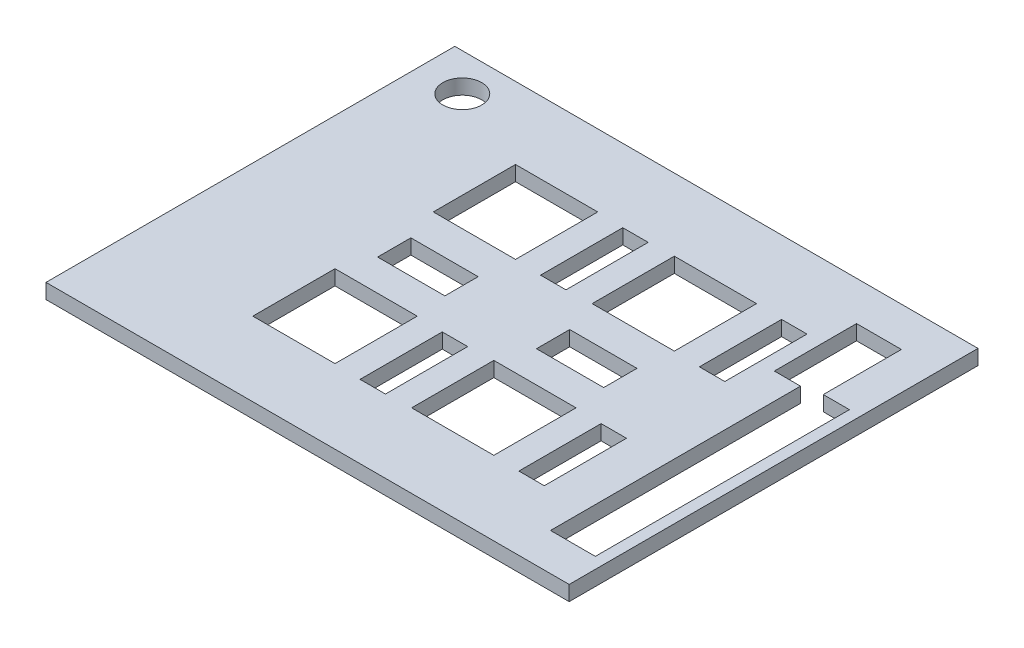
SolidWorks part; units mm, degrees
ref_plane "Front Plane" through (0, 0, 0) normal (0, 0, 1) x (1, 0, 0)
ref_plane "Top Plane" through (0, 0, 0) normal (0, 1, 0) x (1, 0, 0)
ref_plane "Right Plane" through (0, 0, 0) normal (1, 0, 0) x (0, 0, -1)
sketch "Sketch1" plane through (0, 0, 0) normal (0, 1, 0) x (1, 0, 0)
  line L0 (22.75, 28.07) -> (18.75, 28.07)
  line L1 (0, 0) -> (68, 0)
  line L2 (0, 0) -> (0, 52.7)
  line L3 (0, 52.7) -> (68, 52.7)
  line L4 (68, 0) -> (68, 52.7)
  line L5 (0, 0) -> (68, 52.7) construction
  line L6 (0, 52.7) -> (68, 0) construction
  line L7 (17.75, 43.07) -> (26.75, 43.07)
  line L8 (17.75, 43.07) -> (17.75, 34.07)
  line L9 (17.75, 34.07) -> (26.75, 34.07)
  line L10 (26.75, 43.07) -> (26.75, 34.07)
  line L11 (17.75, 43.07) -> (26.75, 34.07) construction
  line L12 (17.75, 34.07) -> (26.75, 43.07) construction
  line L13 (31.75, 33.42) -> (34.15, 33.42)
  line L14 (31.75, 33.42) -> (31.75, 43.42)
  line L15 (31.75, 43.42) -> (34.15, 43.42)
  line L16 (34.15, 33.42) -> (34.15, 43.42)
  line L17 (31.75, 33.42) -> (34.15, 43.42) construction
  line L18 (31.75, 43.42) -> (34.15, 33.42) construction
  line L19 (17.75, 18.92) -> (26.75, 18.92)
  line L20 (17.75, 18.92) -> (17.75, 9.92)
  line L21 (17.75, 9.92) -> (26.75, 9.92)
  line L22 (26.75, 18.92) -> (26.75, 9.92)
  line L23 (17.75, 18.92) -> (26.75, 9.92) construction
  line L24 (17.75, 9.92) -> (26.75, 18.92) construction
  line L25 (39, 34.07) -> (48, 34.07)
  line L26 (39, 34.07) -> (39, 43.07)
  line L27 (39, 43.07) -> (48, 43.07)
  line L28 (48, 34.07) -> (48, 43.07)
  line L29 (39, 34.07) -> (48, 43.07) construction
  line L30 (39, 43.07) -> (48, 34.07) construction
  line L31 (39, 18.92) -> (48, 18.92)
  line L32 (39, 18.92) -> (39, 9.92)
  line L33 (39, 9.92) -> (48, 9.92)
  line L34 (48, 18.92) -> (48, 9.92)
  line L35 (39, 18.92) -> (48, 9.92) construction
  line L36 (39, 9.92) -> (48, 18.92) construction
  line L37 (53, 43.42) -> (55.4, 43.42)
  line L38 (53, 43.42) -> (53, 33.42)
  line L39 (53, 33.42) -> (55.4, 33.42)
  line L40 (55.4, 43.42) -> (55.4, 33.42)
  line L41 (53, 43.42) -> (55.4, 33.42) construction
  line L42 (53, 33.42) -> (55.4, 43.42) construction
  line L43 (31.75, 19.27) -> (34.15, 19.27)
  line L44 (31.75, 19.27) -> (31.75, 9.27)
  line L45 (31.75, 9.27) -> (34.15, 9.27)
  line L46 (34.15, 19.27) -> (34.15, 9.27)
  line L47 (31.75, 19.27) -> (34.15, 9.27) construction
  line L48 (31.75, 9.27) -> (34.15, 19.27) construction
  line L49 (55.4, 19.27) -> (53, 19.27)
  line L50 (55.4, 19.27) -> (55.4, 9.27)
  line L51 (55.4, 9.27) -> (53, 9.27)
  line L52 (53, 19.27) -> (53, 9.27)
  line L53 (55.4, 19.27) -> (53, 9.27) construction
  line L54 (55.4, 9.27) -> (53, 19.27) construction
  line L55 (62, 37.5) -> (67, 37.5)
  line L56 (62, 37.5) -> (62, 4.5)
  line L57 (62, 4.5) -> (67, 4.5)
  line L58 (67, 37.5) -> (67, 4.5)
  line L59 (62, 37.5) -> (67, 4.5) construction
  line L60 (62, 4.5) -> (67, 37.5) construction
  line L61 (58.5, 47.95) -> (63.5, 47.95)
  line L62 (58.5, 47.95) -> (58.5, 37.95)
  line L63 (58.5, 37.95) -> (63.5, 37.95)
  line L64 (63.5, 47.95) -> (63.5, 37.95)
  line L65 (58.5, 47.95) -> (63.5, 37.95) construction
  line L66 (58.5, 37.95) -> (63.5, 47.95) construction
  line L67 (18.75, 24.62) -> (18.75, 28.07)
  line L68 (22.75, 28.07) -> (26.75, 28.07)
  line L69 (22.75, 24.62) -> (26.75, 24.62)
  line L70 (22.75, 24.62) -> (18.75, 24.62)
  line L71 (26.75, 24.62) -> (26.75, 28.07)
  line L73 (40, 28.07) -> (48, 28.07)
  line L74 (40, 28.07) -> (40, 24.62)
  line L75 (40, 24.62) -> (48, 24.62)
  line L76 (48, 28.07) -> (48, 24.62)
  line L77 (40, 28.07) -> (48, 24.62) construction
  line L78 (40, 24.62) -> (48, 28.07) construction
  circle A0 centre (13.75, 50.4) radius 1.5443
  circle A1 centre (13.75, 2.25) radius 1.5443
  circle A2 centre (5, 48.7) radius 1.75
  point P4 (34, 26.35)
  point P16 (22.25, 38.57)
  point P19 (32.95, 38.42)
  point P24 (22.25, 14.42)
  point P29 (43.5, 38.57)
  point P30 (39, 38.57)
  point P35 (43.5, 14.42)
  point P40 (54.2, 38.42)
  point P45 (32.95, 14.27)
  point P50 (54.2, 14.27)
  point P57 (64.5, 21)
  point P62 (61, 42.95)
  point P64 (22.25, 34.07)
  point P74 (44, 26.345)
  dimension "D6" = 3.0886
  dimension "D22" = 3.5
  dimension "D1" = 68
  dimension "D2" = 52.7
  dimension "D3" = 13.75
  dimension "D4" = 48.15
  dimension "D5" = 2.3
  dimension "D7" = 17.75
  dimension "D8" = 9.63
  dimension "D9" = 9
  dimension "D10" = 9
  dimension "D11" = 31.75
  dimension "D12" = 2.4
  dimension "D13" = 9.28
  dimension "D14" = 10
  dimension "D15" = 39
  dimension "D16" = 33.78
  dimension "D17" = 53
  dimension "D18" = 33.43
  dimension "D19" = 10
  dimension "D20" = 4
  dimension "D21" = 5
  dimension "D23" = 62
  dimension "D24" = 5
  dimension "D25" = 15.2
  dimension "D26" = 33
  dimension "D27" = 4.75
  dimension "D28" = 10
  dimension "D29" = 5
  dimension "D30" = 58.5
  dimension "D31" = 6
  dimension "D32" = 3.45
  dimension "D33" = 5
  dimension "D34" = 4
  dimension "D35" = 8
  dimension "D36" = 5
sketch "Sketch2" plane through (0, 0, 0) normal (0, 1, 0) x (1, 0, 0)
  line L14 (69, -1) -> (69, 53.7)
  line L15 (-1, -1) -> (69, -1)
  line L16 (-1, 53.7) -> (-1, -1)
  line L17 (69, 53.7) -> (-1, 53.7)
  line L18 (69, -1) -> (69, 53.7)
  line L19 (-1, -1) -> (69, -1)
  line L20 (-1, 53.7) -> (-1, -1)
  line L21 (69, 53.7) -> (-1, 53.7)
  line L616 (27.75, 33.07) -> (27.75, 44.07)
  line L617 (16.75, 33.07) -> (27.75, 33.07)
  line L618 (16.75, 44.07) -> (16.75, 33.07)
  line L619 (27.75, 44.07) -> (16.75, 44.07)
  line L620 (27.75, 33.07) -> (27.75, 44.07)
  line L621 (16.75, 33.07) -> (27.75, 33.07)
  line L622 (16.75, 44.07) -> (16.75, 33.07)
  line L623 (27.75, 44.07) -> (16.75, 44.07)
  line L634 (49, 33.07) -> (49, 44.07)
  line L635 (38, 33.07) -> (49, 33.07)
  line L636 (38, 44.07) -> (38, 33.07)
  line L637 (49, 44.07) -> (38, 44.07)
  line L638 (49, 33.07) -> (49, 44.07)
  line L639 (38, 33.07) -> (49, 33.07)
  line L640 (38, 44.07) -> (38, 33.07)
  line L641 (49, 44.07) -> (38, 44.07)
  line L652 (27.75, 8.92) -> (27.75, 19.92)
  line L653 (16.75, 8.92) -> (27.75, 8.92)
  line L654 (16.75, 19.92) -> (16.75, 8.92)
  line L655 (27.75, 19.92) -> (16.75, 19.92)
  line L656 (27.75, 8.92) -> (27.75, 19.92)
  line L657 (16.75, 8.92) -> (27.75, 8.92)
  line L658 (16.75, 19.92) -> (16.75, 8.92)
  line L659 (27.75, 19.92) -> (16.75, 19.92)
  line L670 (49, 8.92) -> (49, 19.92)
  line L671 (38, 8.92) -> (49, 8.92)
  line L672 (38, 19.92) -> (38, 8.92)
  line L673 (49, 19.92) -> (38, 19.92)
  line L674 (49, 8.92) -> (49, 19.92)
  line L675 (38, 8.92) -> (49, 8.92)
  line L676 (38, 19.92) -> (38, 8.92)
  line L677 (49, 19.92) -> (38, 19.92)
  line L688 (31.25, 32.92) -> (34.65, 32.92)
  line L689 (34.65, 43.92) -> (31.25, 43.92)
  line L690 (34.65, 32.92) -> (34.65, 43.92)
  line L691 (31.25, 43.92) -> (31.25, 32.92)
  line L692 (31.25, 32.92) -> (34.65, 32.92)
  line L693 (34.65, 43.92) -> (31.25, 43.92)
  line L694 (34.65, 32.92) -> (34.65, 43.92)
  line L695 (31.25, 43.92) -> (31.25, 32.92)
  line L706 (55.9, 32.92) -> (55.9, 43.92)
  line L707 (52.5, 32.92) -> (55.9, 32.92)
  line L708 (52.5, 43.92) -> (52.5, 32.92)
  line L709 (55.9, 43.92) -> (52.5, 43.92)
  line L710 (55.9, 32.92) -> (55.9, 43.92)
  line L711 (52.5, 32.92) -> (55.9, 32.92)
  line L712 (52.5, 43.92) -> (52.5, 32.92)
  line L713 (55.9, 43.92) -> (52.5, 43.92)
  line L724 (34.65, 8.77) -> (34.65, 19.77)
  line L725 (31.25, 8.77) -> (34.65, 8.77)
  line L726 (31.25, 19.77) -> (31.25, 8.77)
  line L727 (34.65, 19.77) -> (31.25, 19.77)
  line L728 (34.65, 8.77) -> (34.65, 19.77)
  line L729 (31.25, 8.77) -> (34.65, 8.77)
  line L730 (31.25, 19.77) -> (31.25, 8.77)
  line L731 (34.65, 19.77) -> (31.25, 19.77)
  line L742 (55.9, 8.77) -> (55.9, 19.77)
  line L743 (52.5, 8.77) -> (55.9, 8.77)
  line L744 (52.5, 19.77) -> (52.5, 8.77)
  line L745 (55.9, 19.77) -> (52.5, 19.77)
  line L746 (55.9, 8.77) -> (55.9, 19.77)
  line L747 (52.5, 8.77) -> (55.9, 8.77)
  line L748 (52.5, 19.77) -> (52.5, 8.77)
  line L749 (55.9, 19.77) -> (52.5, 19.77)
  line L760 (61.5, 4) -> (67.5, 4)
  line L761 (67.5, 4) -> (67.5, 38)
  line L762 (67.5, 38) -> (61.5, 38)
  line L763 (61.5, 38) -> (61.5, 4)
  line L764 (61.5, 4) -> (67.5, 4)
  line L765 (67.5, 4) -> (67.5, 38)
  line L766 (67.5, 38) -> (61.5, 38)
  line L767 (61.5, 38) -> (61.5, 4)
  line L778 (64, 37.45) -> (64, 48.45)
  line L779 (58, 37.45) -> (64, 37.45)
  line L780 (58, 48.45) -> (58, 37.45)
  line L781 (64, 48.45) -> (58, 48.45)
  line L782 (64, 37.45) -> (64, 48.45)
  line L783 (58, 37.45) -> (64, 37.45)
  line L784 (58, 48.45) -> (58, 37.45)
  line L785 (64, 48.45) -> (58, 48.45)
  line L809 (22.75, 28.57) -> (18.25, 28.57)
  line L810 (27.25, 28.57) -> (22.75, 28.57)
  line L811 (27.25, 24.12) -> (27.25, 28.57)
  line L812 (22.75, 24.12) -> (27.25, 24.12)
  line L813 (18.25, 24.12) -> (22.75, 24.12)
  line L814 (18.25, 28.57) -> (18.25, 24.12)
  line L815 (22.75, 28.57) -> (18.25, 28.57)
  line L816 (27.25, 28.57) -> (22.75, 28.57)
  line L817 (27.25, 24.12) -> (27.25, 28.57)
  line L818 (22.75, 24.12) -> (27.25, 24.12)
  line L819 (18.25, 24.12) -> (22.75, 24.12)
  line L820 (18.25, 28.57) -> (18.25, 24.12)
  line L829 (48.5, 24.12) -> (48.5, 28.57)
  line L830 (39.5, 24.12) -> (48.5, 24.12)
  line L831 (39.5, 28.57) -> (39.5, 24.12)
  line L832 (48.5, 28.57) -> (39.5, 28.57)
  line L833 (48.5, 24.12) -> (48.5, 28.57)
  line L834 (39.5, 24.12) -> (48.5, 24.12)
  line L835 (39.5, 28.57) -> (39.5, 24.12)
  line L836 (48.5, 28.57) -> (39.5, 28.57)
  circle A0 centre (5, 48.7) radius 2.6
  dimension "D14" = 5.2
  dimension "D1" = 1
  dimension "D2" = 1
  dimension "D3" = 1
  dimension "D4" = 1
  dimension "D5" = 1
  dimension "D6" = 0.5
  dimension "D7" = 0.5
  dimension "D8" = 0.5
  dimension "D9" = 0.5
  dimension "D10" = 0.5
  dimension "D11" = 0.5
  dimension "D12" = 0.5
  dimension "D13" = 0.5
extrude "Boss-Extrude1" add sketch "Sketch2" along normal blind 2 contours L18 L21 L20 L19 L836 L833 L834 L835 L820 L815 L816 L817 L818 L819 L785 L782 L766 L765 L764 L767 L783 L784 L749 L746 L747 L748 L731 L728 L729 L730 L713 L710 L711 L712 L695 L693 L694 L692 L677 L674 L675 L676 | L657 L656 L659 L658
